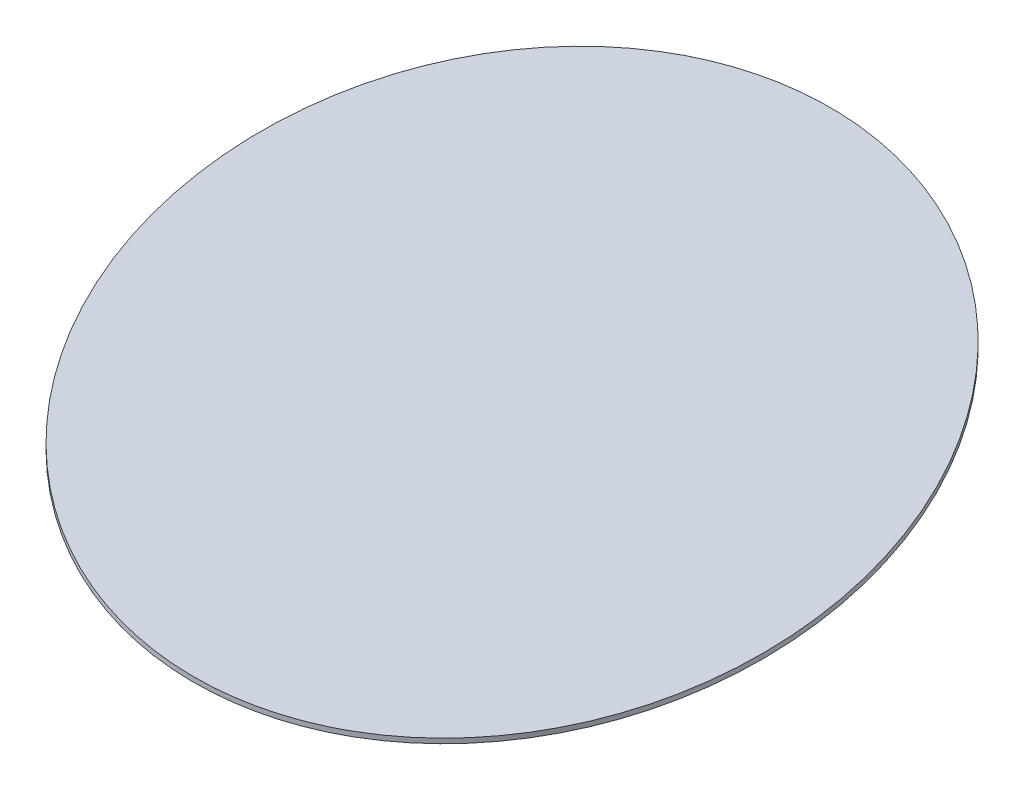
SolidWorks part; units mm, degrees
ref_plane "Front Plane" through (0, 0, 0) normal (0, 0, 1) x (1, 0, 0)
ref_plane "Top Plane" through (0, 0, 0) normal (0, 1, 0) x (1, 0, 0)
ref_plane "Right Plane" through (0, 0, 0) normal (1, 0, 0) x (0, 0, -1)
sketch "Sketch1" plane through (0, 0, 0) normal (0, 1, 0) x (1, 0, 0)
  line L0 (0, 0) -> (-177.5, 307.439) construction
  line L1 (0, 0) -> (229.4967, 132.5) construction
  ellipse E0 centre (0, 0) end of major axis (0, 355) minor radius 265 construction
  ellipse E1 centre (0, 0) end of major axis (177.5, -307.439) minor radius 265
  dimension "D1" = 530
  dimension "D2" = 710
extrude "Boss-Extrude1" add sketch "Sketch1" along normal blind 4
